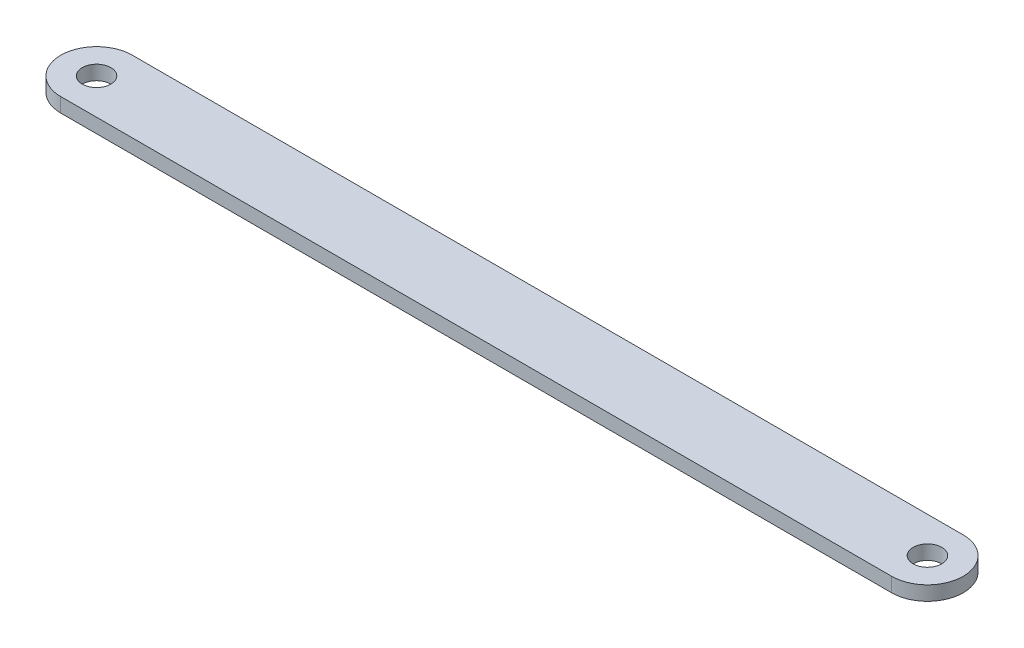
SolidWorks part; units mm, degrees
ref_plane "Front Plane" through (0, 0, 0) normal (0, 0, 1) x (1, 0, 0)
ref_plane "Top Plane" through (0, 0, 0) normal (0, 1, 0) x (1, 0, 0)
ref_plane "Right Plane" through (0, 0, 0) normal (1, 0, 0) x (0, 0, -1)
sketch "Sketch1" plane through (0, 0, 0) normal (0, 1, 0) x (1, 0, 0)
  line L0 (-58, 0) -> (58, 0) construction
  line L1 (-58, 5) -> (58, 5)
  line L2 (-58, -5) -> (58, -5)
  arc A0 (-58, 5) -> (-58, -5) centre (-58, 0) ccw
  arc A1 (58, -5) -> (58, 5) centre (58, 0) ccw
  circle A2 centre (-58, 0) radius 2
  circle A3 centre (58, 0) radius 2
  point P2 (0, 0)
  dimension "D3" = 4
  dimension "D4" = 4
  dimension "D1" = 10
  dimension "D2" = 116
extrude "Boss-Extrude1" add sketch "Sketch1" along normal blind 2
